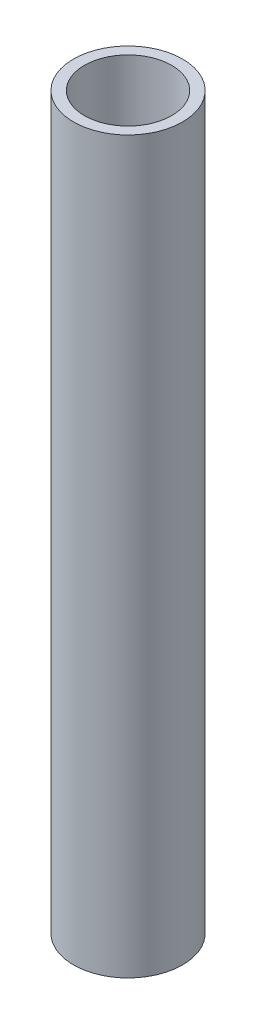
SolidWorks part; units mm, degrees
ref_plane "Спереди" through (0, 0, 0) normal (0, 0, 1) x (1, 0, 0)
ref_plane "Сверху" through (0, 0, 0) normal (0, 1, 0) x (1, 0, 0)
ref_plane "Справа" through (0, 0, 0) normal (1, 0, 0) x (0, 0, -1)
sketch "Эскиз2" plane through (0, 0, 0) normal (1, 0, 0) x (0, 0, -1)
  line L0 (5, 0) -> (15, 0)
  line L1 (15, 0) -> (15, 200.8172)
  line L2 (15, 200.8172) -> (12, 200.8172)
  line L3 (12, 200.8172) -> (12, 10)
  line L4 (12, 10) -> (5, 10)
  line L5 (5, 10) -> (5, 0)
  line L6 (0, 0) -> (0, 208.6643) construction
revolve "Повернуть1" add sketch "Эскиз2" angle 360 about L6
